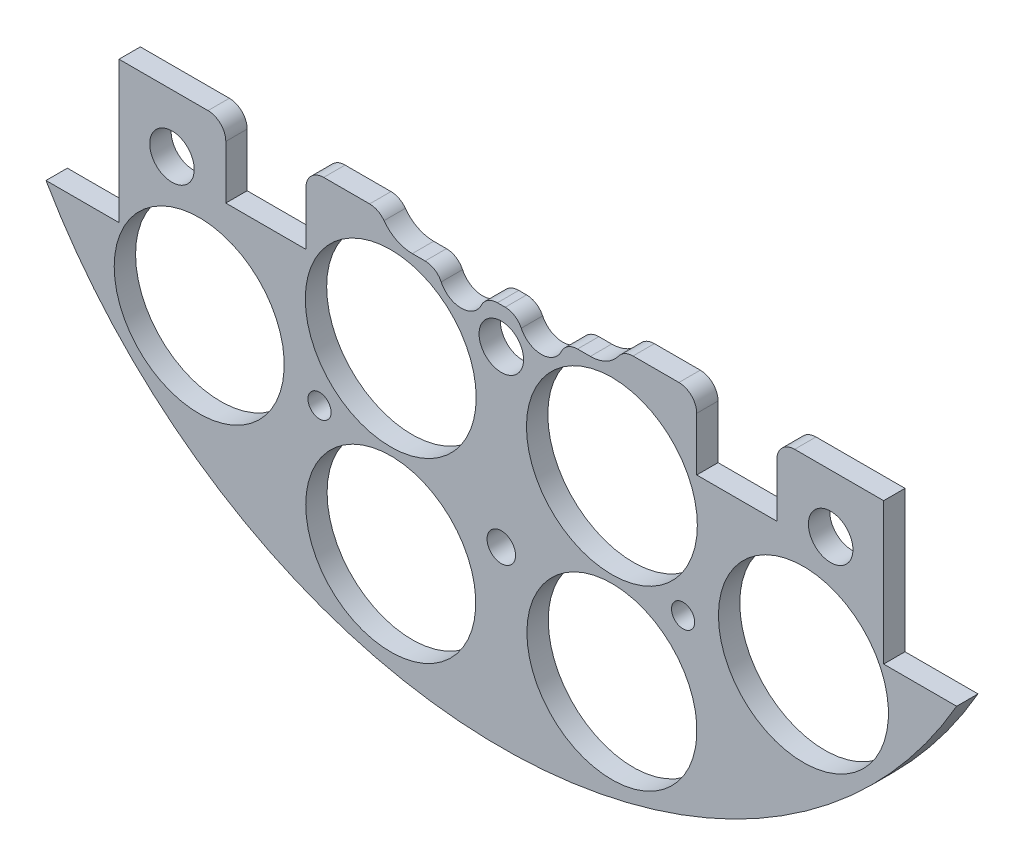
SolidWorks part; units mm, degrees
ref_plane "Front Plane" through (0, 0, 0) normal (0, 0, 1) x (1, 0, 0)
ref_plane "Top Plane" through (0, 0, 0) normal (0, 1, 0) x (1, 0, 0)
ref_plane "Right Plane" through (0, 0, 0) normal (1, 0, 0) x (0, 0, -1)
sketch "Sketch1" plane through (0, 0, 0) normal (0, 0, 1) x (1, 0, 0)
  line L0 (0, 0) -> (-82.1241, 0) construction
  line L1 (0, 0) -> (0, 95.6219) construction
  line L3 (-64.9644, 37.338) -> (-54.5504, 37.338)
  line L5 (-64.9644, -37.338) -> (-54.5504, -37.338)
  line L6 (-54.5504, 37.338) -> (-54.5504, -37.338)
  line L7 (64.9644, -37.338) -> (54.5504, -37.338)
  line L8 (64.9644, 37.338) -> (54.5504, 37.338)
  line L9 (54.5504, 37.338) -> (54.5504, -37.338)
  arc A0 (-64.9644, -37.338) -> (64.9644, -37.338) centre (0, 0) ccw
  circle A1 centre (-46.482, 11.049) radius 1.651
  circle A2 centre (-21.0833, 10.795) radius 1.651
  circle A3 centre (-21.0833, -10.795) radius 1.651
  circle A4 centre (-46.482, -11.049) radius 1.651
  circle A5 centre (46.482, -11.049) radius 1.651
  circle A6 centre (21.0833, -10.795) radius 1.651
  circle A7 centre (21.0833, 10.795) radius 1.651
  circle A8 centre (46.482, 11.049) radius 1.651
  arc A9 (64.9644, 37.338) -> (-64.9644, 37.338) centre (0, 0) ccw
  dimension "D2" = 3.302
  dimension "D3" = 3.302
  dimension "D4" = 25.4
  dimension "D5" = 10.795
  dimension "D10" = 46.482
  dimension "D6" = 74.676
  dimension "D7" = 10.414
  dimension "D8" = 74.93
  dimension "D9" = 74.93
  dimension "D11" = 37.338
extrude "Boss-Extrude2" add sketch "Sketch1" along normal blind 3.048
sketch "Sketch2" plane through (0, 0, 3.048) normal (0, 0, 1) x (1, 0, 0)
  line L0 (0, 68.58) -> (0, 55.88) construction
  line L1 (-9.525, 68.58) -> (9.525, 68.58)
  line L2 (-9.525, 68.58) -> (-9.525, 55.88)
  line L3 (-9.525, 55.88) -> (9.525, 55.88)
  line L4 (9.525, 68.58) -> (9.525, 55.88)
  line L5 (-9.525, 62.23) -> (9.525, 62.23) construction
  arc A0 (64.9644, 37.338) -> (-64.9644, 37.338) centre (0, 0) ccw construction
  circle A1 centre (-21.0833, 10.795) radius 1.651 construction
  circle A2 centre (21.0833, 10.795) radius 1.651 construction
  circle A3 centre (-6.731, 62.23) radius 1.143
  circle A4 centre (6.731, 62.23) radius 1.143
  dimension "D4" = 2.286
  dimension "D5" = 0
  dimension "D6" = 6.731
  dimension "D1" = 19.05
  dimension "D2" = 12.7
  dimension "D3" = 55.88
extrude "Cut-Extrude1" cut sketch "Sketch2" against normal through all contours A3 | A4
sketch "Sketch3" plane through (0, 0, 0) normal (0, 0, -1) x (-1, 0, 0)
  line L0 (0, 0) -> (0, -116.2908) construction
  line L1 (0, 0) -> (-153.8039, 0) construction
  line L2 (0, 0) -> (15.2681, -56.9814) construction
  line L3 (0, 0) -> (15.2302, -26.3795) construction
  circle A0 centre (-15.7776, -58.8828) radius 12.1285
  circle A3 centre (15.7776, -58.8828) radius 12.1285
  circle A4 centre (-43.1052, -43.1052) radius 12.1285
  circle A7 centre (19.05, 32.9956) radius 12.1285
  circle A8 centre (-43.1052, 43.1052) radius 12.1285
  circle A11 centre (43.1052, 43.1052) radius 12.1285
  circle A12 centre (-19.05, 32.9956) radius 12.1285
  circle A14 centre (43.1052, -43.1052) radius 12.1285
  circle A33 centre (58.8828, -15.7776) radius 12.1285 [skipped]
  circle A34 centre (58.8828, 15.7776) radius 12.1285 [skipped]
  circle A35 centre (-58.8828, 15.7776) radius 12.1285 [skipped]
  circle A36 centre (-58.8828, -15.7776) radius 12.1285 [skipped]
  circle A37 centre (-15.7776, 58.8828) radius 12.1285 [skipped]
  circle A38 centre (15.7776, 58.8828) radius 12.1285 [skipped]
  point P36 (0, 0)
  point P53 (0, 0)
  point P55 (0, 0)
  dimension "D3" = 0
  dimension "D4" = 15
  dimension "D5" = 24.257
  dimension "D7" = 12
  dimension "D9" = 30
extrude "Cut-Extrude2" cut sketch "Sketch3" against normal through all
sketch "Sketch4" plane through (0, 0, 0) normal (0, 0, -1) x (-1, 0, 0)
  line L1 (-15.7702, 56.3138) -> (12.7925, 56.3138)
  line L2 (-15.7702, 56.3138) -> (-15.7702, 67.9913)
  line L3 (-15.7702, 67.9913) -> (12.7925, 67.9913)
  line L4 (12.7925, 56.3138) -> (12.7925, 67.9913)
extrude "Boss-Extrude3" add sketch "Sketch4" against normal up to surface (3.048 mm away) up to face at (-55.2337, -43.1052, 3.048)
sketch "Sketch5" plane through (0, 0, 0) normal (0, 0, -1) x (-1, 0, 0)
  line L1 (-85.044, -17.145) -> (131.6774, -17.145)
  line L2 (-85.044, -17.145) -> (-85.044, 113.4242)
  line L3 (-85.044, 113.4242) -> (131.6774, 113.4242)
  line L4 (131.6774, -17.145) -> (131.6774, 113.4242)
  circle A0 centre (-21.0833, -10.795) radius 1.651 construction
  dimension "D1" = 6.35
extrude "Cut-Extrude4" cut sketch "Sketch5" against normal through all contours L2 L3 L4 L1
sketch "Sketch6" plane through (0, 0, 0) normal (0, 0, -1) x (-1, 0, 0)
  line L1 (-54.5504, -17.145) -> (54.5504, -17.145) construction
  line L2 (-2.3812, -32.131) -> (-6.3812, -32.131)
  line L3 (-6.3812, -32.131) -> (-6.3812, -17.145)
  line L4 (-6.3812, -17.145) -> (-9.3812, -17.145)
  line L5 (-9.3812, -17.145) -> (-9.3812, -34.131)
  line L6 (2.3813, -59.563) -> (-2.3812, -59.563)
  line L7 (2.3813, -59.563) -> (2.3813, -32.131)
  line L8 (2.3813, -32.131) -> (-2.3812, -32.131)
  line L9 (-2.3812, -59.563) -> (-2.3812, -32.131)
  line L10 (-9.3812, -34.131) -> (-2.3812, -34.131)
  line M13 (54.5504, -17.145) -> (-54.5504, -17.145)
  dimension "D1" = 42.418
  dimension "D2" = 3
  dimension "D3" = 2
  dimension "D4" = 4
  dimension "D5" = 27.432
  dimension "D6" = 4.7625
extrude "Cut-Extrude5" cut sketch "Sketch6" against normal through all contours L9 L6 L7 L8 | L5 L10 L9 L2 L3 M13
extrude "Cut-Extrude6" cut sketch "Sketch7" against normal through all both and the other way through all
sketch "Sketch7" plane through (31.3134, 132.614, -9.525) normal (0, 0, -1) x (0, 1, 0)
  line L0 (-132.614, -31.3134) -> (-132.614, 57.8454) construction
  line L1 (-132.614, -31.3134) -> (-222.516, -31.3134) construction
  circle A0 centre (-158.014, 14.4066) radius 3.175
  circle A1 centre (-173.254, -31.3134) radius 3.175
  circle A3 centre (-158.014, -77.0334) radius 3.175
  circle A4 centre (-107.214, -77.0334) radius 3.175
  circle A5 centre (-91.974, -31.3134) radius 3.175
  circle A6 centre (-107.214, 14.4066) radius 3.175
extrude "Cut-Extrude7" cut sketch "Sketch8" against normal blind 29.21
sketch "Sketch8" plane through (31.3134, 132.559, -6.35) normal (0, 0, -1) x (0, 1, 0)
  line L0 (-132.559, -31.3134) -> (6.1626, -31.3134) construction
  line L2 (-132.559, -31.3134) -> (-132.559, -122.6589) construction
  circle A0 centre (-190.979, 2.9766) radius 1.651
  circle A2 centre (-154.784, -31.3134) radius 1.651
  circle A3 centre (-190.979, -65.6034) radius 1.651
  circle A4 centre (-110.334, -31.3134) radius 1.651
  circle A5 centre (-74.139, -65.6034) radius 1.651
  circle A6 centre (-74.139, 2.9766) radius 1.651
sketch "Sketch10" plane through (0, 0, 0) normal (0, 0, -1) x (-1, 0, 0)
  line L0 (-54.5504, -17.145) -> (-9.3812, -17.145) construction
  line L1 (-39.3104, -17.145) -> (-27.8804, -17.145)
  line L2 (-39.3104, -17.145) -> (-39.3104, -27.305)
  line L3 (-39.3104, -27.305) -> (-27.8804, -27.305)
  line L4 (-27.8804, -17.145) -> (-27.8804, -27.305)
  line L5 (-6.3812, -17.145) -> (54.5504, -17.145) construction
  line L6 (27.8804, -17.145) -> (39.3104, -17.145)
  line L7 (27.8804, -17.145) -> (27.8804, -27.305)
  line L8 (27.8804, -27.305) -> (39.3104, -27.305)
  line L9 (39.3104, -17.145) -> (39.3104, -27.305)
  line L10 (-54.5504, -37.338) -> (-54.5504, -17.145) construction
  line L11 (0, -3.5331) -> (0, -80.5859) construction
  dimension "D1" = 10.16
  dimension "D2" = 11.43
  dimension "D3" = 15.24
extrude "Cut-Extrude9" cut sketch "Sketch10" against normal through all
fillet "Fillet1" radius 6 1 edges at (6.3812, -32.131, 1.524)
fillet "Fillet2" radius 6 1 edges at (2.3812, -34.131, 1.524)
extrude "Cut-Extrude65" cut sketch "Sketch66" against normal blind 97.79
sketch "Sketch66" plane through (30.092, 4.0835, -16.1925) normal (0, 0, -1) x (-1, 0, 0)
  line L0 (30.092, -29.4835) -> (30.092, 6.2385) construction
  circle A0 centre (4.1544, -49.7288) radius 1.651
  circle A4 centre (56.0296, -49.7288) radius 1.651
  circle A5 centre (4.1544, 41.3825) radius 1.651
  circle A9 centre (56.0296, 41.3825) radius 1.651
extrude "Cut-Extrude119" cut sketch "Sketch120" against normal blind 48.768 and the other way blind 103.378
sketch "Sketch120" plane through (30.092, 4.0835, 19.939) normal (0, 0, -1) x (-1, 0, 0)
  line L0 (30.092, -4.0835) -> (148.6336, -4.0835) construction
  line L1 (30.092, -4.0835) -> (30.092, 90.452) construction
  circle A0 centre (-16.898, 21.3165) radius 3.175
  circle A1 centre (77.082, 21.3165) radius 3.175
  circle A2 centre (30.092, 21.3165) radius 3.175
  circle A4 centre (77.082, -29.4835) radius 3.175
  circle A5 centre (30.092, -29.4835) radius 3.175
  circle A6 centre (-16.898, -29.4835) radius 3.175
sketch "Sketch13" plane through (0, 0, 0) normal (0, 0, -1) x (-1, 0, 0)
  line L0 (0, 0) -> (0, 51.5587) construction
  line L1 (-9.3812, -17.145) -> (-9.3812, -34.131) construction
  line L2 (-12.7, -20.24) -> (-8.889, -20.24)
  line L3 (-2.541, -20.24) -> (2.541, -20.24)
  line L4 (-1.0625, -15.24) -> (7.7, -15.24)
  line L5 (8.889, -20.24) -> (12.7, -20.24)
  arc A0 (-9.3812, -11.5002) -> (-12.7, -20.24) centre (-12.7, -15.24) ccw
  arc A1 (7.7, -15.24) -> (12.7, -20.24) centre (12.7, -15.24) cw
  arc A2 (-9.3812, -11.5002) -> (-1.0625, -15.24) centre (-6.0625, -15.24) cw
  arc A3 (-8.889, -20.24) -> (-2.541, -20.24) centre (-5.715, -20.32) ccw
  arc A4 (2.541, -20.24) -> (8.889, -20.24) centre (5.715, -20.32) ccw
  dimension "D1" = 10
  dimension "D4" = 11.43
  dimension "D5" = 6.35
  dimension "D6" = 6.35
  dimension "D2" = 12.7
  dimension "D3" = 15.24
  dimension "D7" = 5.715
  dimension "D8" = 20.32
extrude "Cut-Extrude12" cut sketch "Sketch13" against normal blind 10
fillet "Fillet3" radius 2.54 11 edges at (-39.3104, -17.145, 1.524) (-27.8804, -17.145, 1.524) (-17.3229, -17.145, 1.524) (-8.889, -20.24, 1.524) (2.541, -20.24, 1.524) (-2.541, -20.24, 1.524) (6.3812, -23.4243, 1.524) (9.3812, -20.24, 1.524) (17.3229, -17.145, 1.524) (27.8804, -17.145, 1.524) (39.3104, -17.145, 1.524)
sketch "Sketch121" plane through (0, 0, 3.048) normal (0, 0, 1) x (1, 0, 0)
  line L0 (2.8911, -60.5154) -> (4.3227, -42.1248)
  line L1 (4.3227, -42.1248) -> (14.0135, -30.5618)
  line L2 (14.0135, -30.5618) -> (14.7608, -20.9621)
  line L4 (4.9429, -26.8451) -> (2.8911, -29.631)
  line L5 (2.8911, -29.631) -> (-4.1568, -31.553)
  line L6 (-4.1568, -31.553) -> (-2.9455, -62.1673)
  line L7 (-2.9455, -62.1673) -> (2.8911, -60.5154)
  line L8 (0, -25.4) -> (0, 2.9351) construction
  line L10 (14.7608, -20.9621) -> (16.7388, -18.1876)
  line L11 (10.8735, -20.24) -> (12.7, -20.24)
  line L12 (4.9429, -26.8451) -> (2.8492, -21.6867)
  arc A0 (-8.5808, -21.6867) -> (-2.8492, -21.6867) centre (-5.715, -20.32) ccw construction
  arc A2 (8.5808, -21.6867) -> (2.8492, -21.6867) centre (5.715, -20.32) cw
  arc A3 (-16.7388, -18.1876) -> (-12.7, -20.24) centre (-12.7, -15.24) ccw construction
  arc A4 (-8.5808, -21.6867) -> (-10.8735, -20.24) centre (-10.8735, -22.78) ccw construction
  arc A7 (8.5808, -21.6867) -> (10.8735, -20.24) centre (10.8735, -22.78) cw
  arc A8 (16.7388, -18.1876) -> (12.7, -20.24) centre (12.7, -15.24) cw
extrude "Boss-Extrude4" add sketch "Sketch121" against normal blind 3.048
sketch "Sketch122" plane through (0, 0, 3.048) normal (0, 0, 1) x (1, 0, 0)
  line L0 (25.3404, -17.145) -> (18.7904, -17.145) construction
  circle A0 centre (0, -50.165) radius 2.032
  dimension "D1" = 4.064
  dimension "D2" = 33.02
extrude "Cut-Extrude120" cut sketch "Sketch122" against normal blind 27.305
sketch "Sketch123" plane through (0, 0, 0) normal (0, 0, -1) x (-1, 0, 0)
  circle A0 centre (-15.7776, -33.4828) radius 12.192
  circle A1 centre (15.7776, -33.4828) radius 12.192
  circle A2 centre (-15.7776, -58.8828) radius 12.1285 construction
  circle A3 centre (15.7776, -58.8828) radius 12.1285 construction
  dimension "D1" = 24.384
  dimension "D2" = 24.384
  dimension "D5" = 0
  dimension "D3" = 25.4
  dimension "D4" = 25.4
  dimension "D6" = 0
extrude "Cut-Extrude121" cut sketch "Sketch123" against normal blind 19.05
